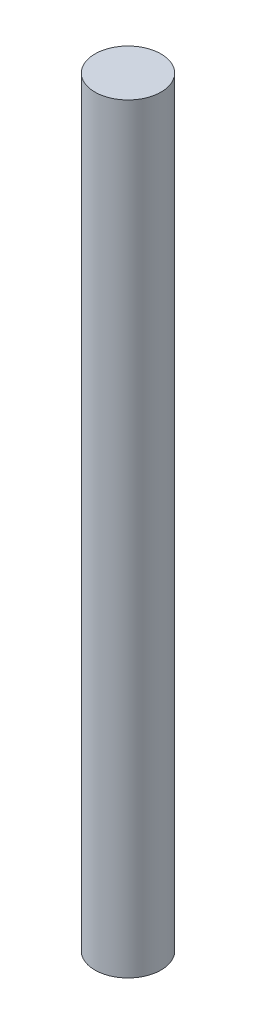
SolidWorks part; units mm, degrees
ref_plane "Спереди" through (0, 0, 0) normal (0, 0, 1) x (1, 0, 0)
ref_plane "Сверху" through (0, 0, 0) normal (0, 1, 0) x (1, 0, 0)
ref_plane "Справа" through (0, 0, 0) normal (1, 0, 0) x (0, 0, -1)
sketch "Эскиз1" plane through (0, 0, 0) normal (0, 1, 0) x (1, 0, 0)
  circle A0 centre (0, 0) radius 1
extrude "Бобышка-Вытянуть1" add sketch "Эскиз1" along normal blind 23
